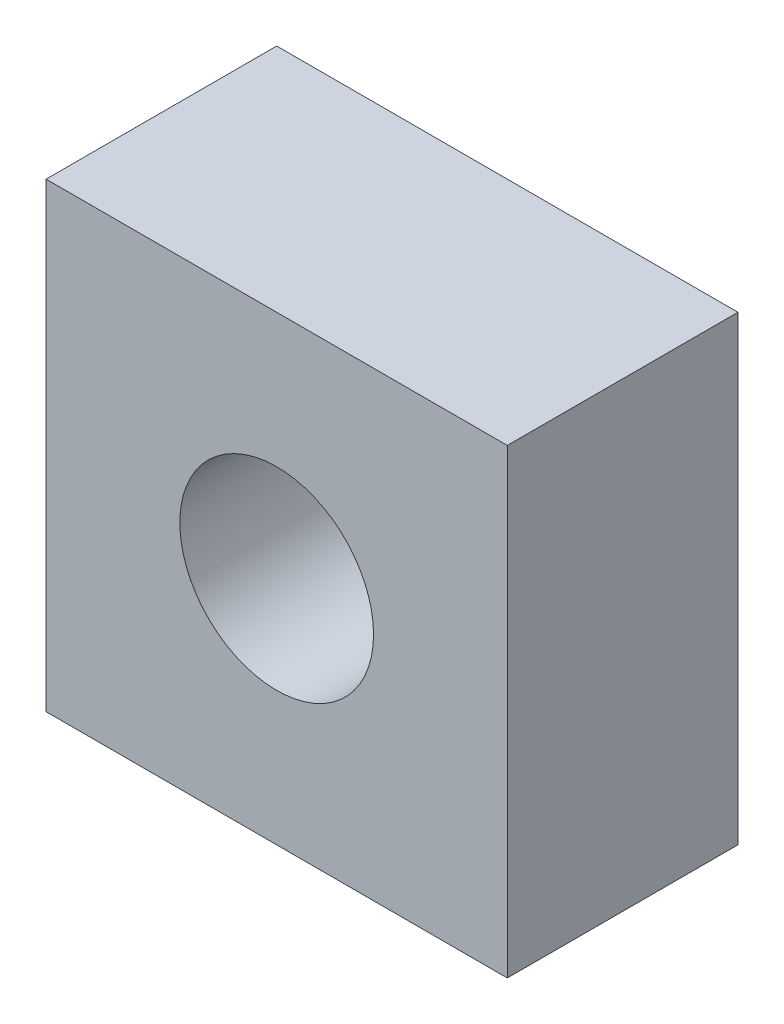
SolidWorks part; units mm, degrees
ref_plane "Front Plane" through (0, 0, 0) normal (0, 0, 1) x (1, 0, 0)
ref_plane "Top Plane" through (0, 0, 0) normal (0, 1, 0) x (1, 0, 0)
ref_plane "Right Plane" through (0, 0, 0) normal (1, 0, 0) x (0, 0, -1)
sketch "Sketch1" plane through (0, 0, 0) normal (0, 0, 1) x (1, 0, 0)
  line L1 (0, 0) -> (-10, 0)
  line L2 (0, 0) -> (0, 10)
  line L3 (0, 10) -> (-10, 10)
  line L4 (-10, 0) -> (-10, 10)
  circle A0 centre (-5, 5) radius 2.1
  dimension "D3" = 4.2
  dimension "D1" = 10
  dimension "D2" = 10
extrude "Boss-Extrude1" add sketch "Sketch1" along normal blind 5
